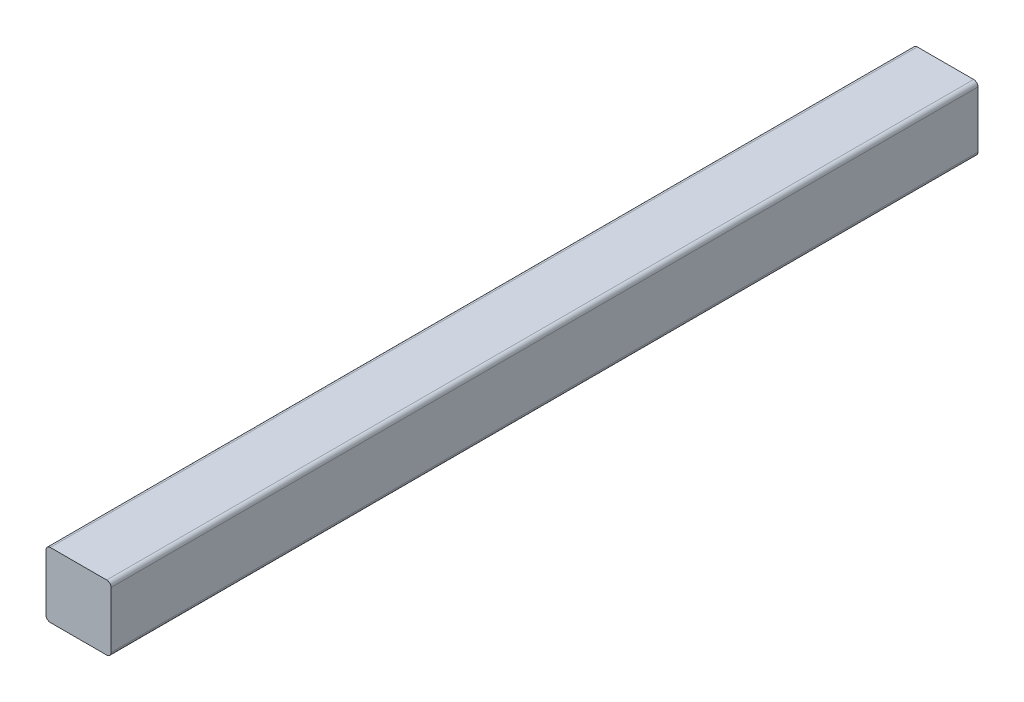
SolidWorks part; units mm, degrees
ref_plane "Front Plane" through (0, 0, 0) normal (0, 0, 1) x (1, 0, 0)
ref_plane "Top Plane" through (0, 0, 0) normal (0, 1, 0) x (1, 0, 0)
ref_plane "Right Plane" through (0, 0, 0) normal (1, 0, 0) x (0, 0, -1)
sketch "Sketch1" plane through (0, 0, 0) normal (0, 0, 1) x (1, 0, 0)
  line L0 (2, 0) -> (28, 0)
  line L1 (30, 2) -> (30, 28)
  line L2 (28, 30) -> (2, 30)
  line L3 (0, 28) -> (0, 2)
  arc A0 (2, 0) -> (0, 2) centre (2, 2) cw
  arc A1 (30, 2) -> (28, 0) centre (28, 2) cw
  arc A2 (28, 30) -> (30, 28) centre (28, 28) cw
  arc A3 (0, 28) -> (2, 30) centre (2, 28) cw
  point P7 (0, 0)
  dimension "D1" = 2
  dimension "D2" = 2
  dimension "D3" = 2
  dimension "D4" = 2
sketch "Sketch3" plane through (0, 0, 0) normal (0, 0, 1) x (1, 0, 0)
  line L0 (2, 0) -> (28, 0)
  line L1 (30, 2) -> (30, 28)
  line L2 (28, 30) -> (2, 30)
  line L3 (0, 28) -> (0, 2)
  arc A0 (2, 0) -> (0, 2) centre (2, 2) cw
  arc A1 (30, 2) -> (28, 0) centre (28, 2) cw
  arc A2 (28, 30) -> (30, 28) centre (28, 28) cw
  arc A3 (0, 28) -> (2, 30) centre (2, 28) cw
  dimension "D1" = 2
extrude "Boss-Extrude1" add sketch "Sketch3" along normal blind 400
